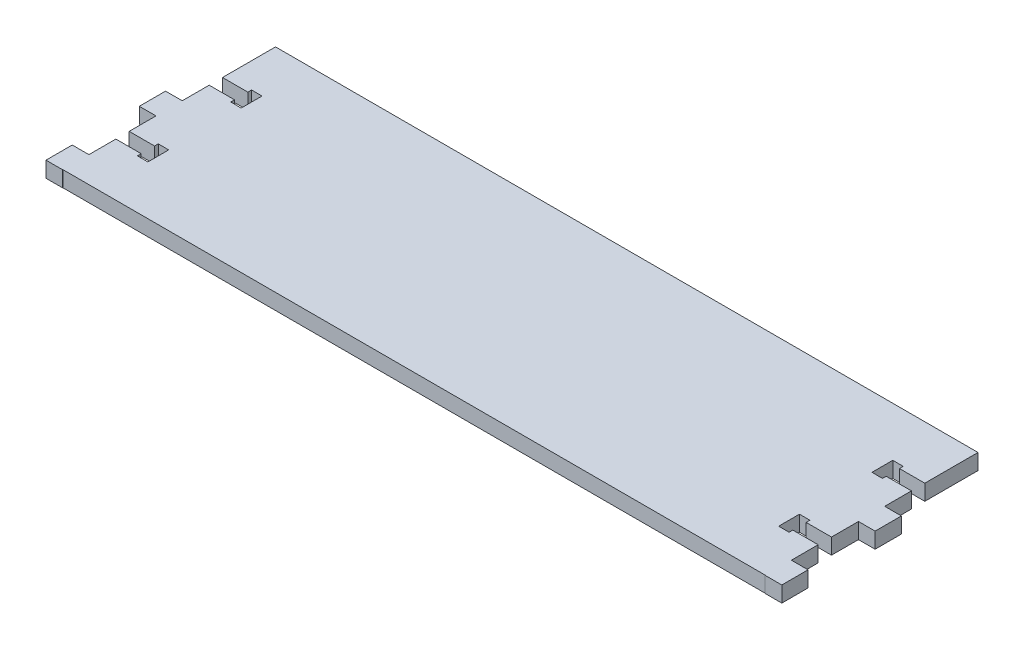
SolidWorks part; units mm, degrees
ref_plane "Front Plane" through (0, 0, 0) normal (0, 0, 1) x (1, 0, 0)
ref_plane "Top Plane" through (0, 0, 0) normal (0, 1, 0) x (1, 0, 0)
ref_plane "Right Plane" through (0, 0, 0) normal (1, 0, 0) x (0, 0, -1)
sketch "Sketch1" plane through (0, 0, 0) normal (0, 1, 0) x (1, 0, 0)
  line L0 (213.9688, 32.4374) -> (225.4509, 32.4374) construction
  line L1 (-40.0952, 55.2174) -> (227.6208, 55.2174)
  line L2 (-40.0952, 55.2174) -> (-40.0952, -25.8086)
  line L3 (-40.0952, -25.8086) -> (227.6208, -25.8086)
  line L4 (227.6208, 55.2174) -> (227.6208, -25.8086)
  line L5 (213.9688, -3.1226) -> (222.86, -3.1226) construction
  line L6 (-26.4432, 32.4374) -> (-36.9752, 32.4374) construction
  line L7 (-26.4432, -3.1226) -> (-38.5529, -3.1226) construction
  line B0 (-40.0952, 29.9338) -> (-30.4432, 29.9338)
  line B1 (-30.4432, 29.9338) -> (-30.4432, 28.5051)
  line B2 (-30.4432, 28.5051) -> (-26.4432, 28.4686)
  line B3 (-26.4432, 28.4686) -> (-26.4432, 36.4061)
  line B4 (-26.4432, 36.4061) -> (-30.4432, 36.4426)
  line B5 (-30.4432, 36.4426) -> (-30.4432, 35.0138)
  line B6 (-30.4432, 35.0138) -> (-40.0952, 35.0138)
  line B7 (227.6208, -0.6191) -> (217.9688, -0.6191)
  line B8 (217.9688, -0.6191) -> (217.9688, 0.8096)
  line B9 (217.9688, 0.8096) -> (213.9688, 0.8461)
  line B10 (213.9688, 0.8461) -> (213.9688, -7.0914)
  line B11 (213.9688, -7.0914) -> (217.9688, -7.1279)
  line B12 (217.9688, -7.1279) -> (217.9688, -5.6991)
  line B13 (217.9688, -5.6991) -> (227.6208, -5.6991)
  line B14 (123.1945, 152.9031) -> (123.1945, 143.2511)
  line B15 (123.1945, 143.2511) -> (121.7658, 143.2511)
  line B16 (121.7658, 143.2511) -> (121.7293, 139.2511)
  line B17 (121.7293, 139.2511) -> (129.6668, 139.2511)
  line B18 (129.6668, 139.2511) -> (129.7033, 143.2511)
  line B19 (129.7033, 143.2511) -> (128.2745, 143.2511)
  line B20 (128.2745, 143.2511) -> (128.2745, 152.9031)
  line B21 (184.9705, 152.9031) -> (184.9705, 143.2511)
  line B22 (184.9705, 143.2511) -> (183.5417, 143.2511)
  line B23 (183.5417, 143.2511) -> (183.5052, 139.2511)
  line B24 (183.5052, 139.2511) -> (191.4427, 139.2511)
  line B25 (191.4427, 139.2511) -> (191.4792, 143.2511)
  line B26 (191.4792, 143.2511) -> (190.0505, 143.2511)
  line B27 (190.0505, 143.2511) -> (190.0505, 152.9031)
  line B28 (-40.0952, -5.6262) -> (-30.4432, -5.6262)
  line B29 (-30.4432, -5.6262) -> (-30.4432, -7.0549)
  line B30 (-30.4432, -7.0549) -> (-26.4432, -7.0914)
  line B31 (-26.4432, -7.0914) -> (-26.4432, 0.8461)
  line B32 (-26.4432, 0.8461) -> (-30.4432, 0.8826)
  line B33 (-30.4432, 0.8826) -> (-30.4432, -0.5462)
  line B34 (-30.4432, -0.5462) -> (-40.0952, -0.5462)
  line B35 (227.6208, 34.9409) -> (217.9688, 34.9409)
  line B36 (217.9688, 34.9409) -> (217.9688, 36.3696)
  line B37 (217.9688, 36.3696) -> (213.9688, 36.4061)
  line B38 (213.9688, 36.4061) -> (213.9688, 28.4686)
  line B39 (213.9688, 28.4686) -> (217.9688, 28.4321)
  line B40 (217.9688, 28.4321) -> (217.9688, 29.8609)
  line B41 (217.9688, 29.8609) -> (227.6208, 29.8609)
  line B42 (-46.4452, 50.2174) -> (-40.0952, 50.2174) construction
  line B43 (-46.4452, 45.2174) -> (-46.4452, 55.2174)
  line B44 (-46.4452, 45.2174) -> (-40.0952, 45.2174)
  line B45 (-40.0952, 45.2174) -> (-40.0952, 55.2174)
  line B46 (-46.4452, 55.2174) -> (-40.0952, 55.2174)
  line B47 (-46.4452, 14.6574) -> (-40.0952, 14.6574) construction
  line B48 (-46.4452, 9.6574) -> (-46.4452, 19.6574)
  line B49 (-46.4452, 9.6574) -> (-40.0952, 9.6574)
  line B50 (-40.0952, 9.6574) -> (-40.0952, 19.6574)
  line B51 (-46.4452, 19.6574) -> (-40.0952, 19.6574)
  line B52 (227.6208, 50.2174) -> (233.9708, 50.2174) construction
  line B53 (227.6208, 45.2174) -> (227.6208, 55.2174)
  line B54 (227.6208, 45.2174) -> (233.9708, 45.2174)
  line B55 (233.9708, 45.2174) -> (233.9708, 55.2174)
  line B56 (227.6208, 55.2174) -> (233.9708, 55.2174)
  line B57 (-46.4452, -20.9026) -> (-40.0952, -20.9026) construction
  line B58 (-46.4452, -25.9026) -> (-46.4452, -15.9026)
  line B59 (-46.4452, -25.9026) -> (-40.0952, -25.9026)
  line B60 (-40.0952, -25.9026) -> (-40.0952, -15.9026)
  line B61 (-46.4452, -15.9026) -> (-40.0952, -15.9026)
  line B62 (227.6208, -20.9026) -> (233.9708, -20.9026) construction
  line B63 (227.6208, -25.9026) -> (227.6208, -15.9026)
  line B64 (227.6208, -25.9026) -> (233.9708, -25.9026)
  line B65 (233.9708, -25.9026) -> (233.9708, -15.9026)
  line B66 (227.6208, -15.9026) -> (233.9708, -15.9026)
  line B67 (227.6208, 14.6574) -> (233.9708, 14.6574) construction
  line B68 (227.6208, 9.6574) -> (227.6208, 19.6574)
  line B69 (227.6208, 9.6574) -> (233.9708, 9.6574)
  line B70 (233.9708, 9.6574) -> (233.9708, 19.6574)
  line B71 (227.6208, 19.6574) -> (233.9708, 19.6574)
  dimension "D1" = 81.026
  dimension "D2" = 267.716
  dimension "D3" = 17.78
  dimension "D4" = 17.78
  dimension "D5" = 17.78
  dimension "D6" = 17.78
  dimension "D7" = 17.78
  dimension "D8" = 17.78
  dimension "D9" = 17.78
  dimension "D10" = 17.78
sketch_block_instance "screwblock-1"
sketch_block "screwblock" parameters "D1"=4.2151, "D2"=10.103, "D3"=7.4845, "D4"=1.829
sketch_block_instance "screwblock-2"
sketch_block_instance "screwblock-3"
sketch_block_instance "screwblock-4"
sketch_block_instance "screwblock-5"
sketch_block_instance "screwblock-6"
sketch_block_instance "extrusionblock-1"
sketch_block "extrusionblock" parameters "D1"=6.35, "D2"=10
sketch_block_instance "extrusionblock-2"
sketch_block_instance "extrusionblock-3"
sketch_block_instance "extrusionblock-4"
sketch_block_instance "extrusionblock-6"
sketch_block_instance "extrusionblock-7"
extrude "Extrude1" add sketch "Sketch1" along normal blind 5.9944 contours B51 B48 B49 L2 | B41 B40 B39 B38 B37 B36 B35 L4 L1 L2 B6 B5 B4 B3 B2 B1 B0 B34 B33 B32 B31 B30 B29 B28 L3 B13 B12 B11 B10 B9 B8 B7 | B61 B58 B59 B60 L2 | B66 L4 B63 B64 B65 | B71 L4 B69 B70
